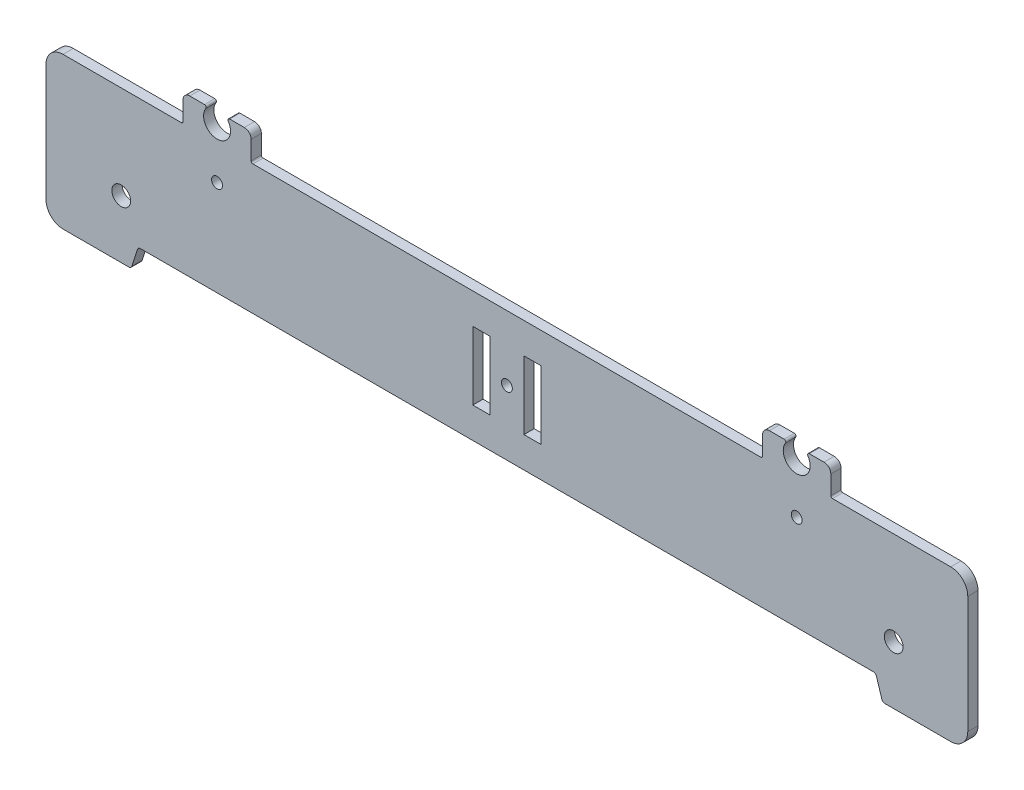
SolidWorks part; units mm, degrees
ref_plane "Alzado" through (0, 0, 0) normal (0, 0, 1) x (1, 0, 0)
ref_plane "Planta" through (0, 0, 0) normal (0, 1, 0) x (1, 0, 0)
ref_plane "Vista lateral" through (0, 0, 0) normal (1, 0, 0) x (0, 0, -1)
sketch "Model" plane through (0, 0, 0) normal (0, 0, 1) x (1, 0, 0)
  line L0 (144.0398, 7.6866) -> (36.5996, 7.689)
  line L1 (35.6453, 6.9878) -> (34.0844, 2.0026)
  line L2 (33.1301, 1.3014) -> (13.8648, 1.3014)
  line L3 (8.8648, 6.3014) -> (8.8648, 40.689)
  line L4 (13.8648, 45.689) -> (18.8648, 45.689)
  line L5 (18.8648, 45.689) -> (48.5373, 45.689)
  line L6 (49.0373, 46.189) -> (49.0373, 51.687)
  line L7 (51.0373, 53.687) -> (55.3535, 53.687)
  line L8 (62.7212, 53.687) -> (67.0373, 53.687)
  line L9 (69.0373, 51.687) -> (69.0373, 46.189)
  line L10 (69.5373, 45.689) -> (144.0398, 45.689)
  line L11 (144.0398, 45.689) -> (218.5423, 45.689)
  line L12 (219.0423, 46.189) -> (219.0423, 51.687)
  line L13 (221.0423, 53.687) -> (225.3585, 53.687)
  line L14 (232.7262, 53.687) -> (237.0423, 53.687)
  line L15 (239.0423, 51.687) -> (239.0423, 46.189)
  line L16 (239.5423, 45.689) -> (269.2148, 45.689)
  line L17 (269.2148, 45.689) -> (274.2148, 45.689)
  line L18 (279.2148, 40.689) -> (279.2148, 6.3014)
  line L19 (274.2148, 1.3014) -> (254.9496, 1.3014)
  line L20 (253.9953, 2.0026) -> (252.4344, 6.9878)
  line L21 (251.4801, 7.689) -> (144.0398, 7.6866)
  line L22 (154.0398, 36.6878) -> (149.0398, 36.6878)
  line L23 (149.0398, 36.6878) -> (149.0398, 16.6878)
  line L24 (149.0398, 16.6878) -> (154.0398, 16.6878)
  line L25 (154.0398, 16.6878) -> (154.0398, 26.6878)
  line L26 (154.0398, 26.6878) -> (154.0398, 36.6878)
  line L27 (134.0398, 36.6878) -> (139.0398, 36.6878)
  line L28 (139.0398, 36.6878) -> (139.0398, 16.6878)
  line L29 (139.0398, 16.6878) -> (134.0398, 16.6878)
  line L30 (134.0398, 16.6878) -> (134.0398, 26.6878)
  line L31 (134.0398, 26.6878) -> (134.0398, 36.6878)
  circle A0 centre (59.0373, 35.6907) radius 1.6
  circle A1 centre (144.0398, 26.6878) radius 1.6
  circle A2 centre (229.0423, 35.6907) radius 1.6
  circle A3 centre (144.0398, 26.6878) radius 1.6
  circle A4 centre (30.9257, 18.3014) radius 2.75
  circle A5 centre (257.4839, 18.3014) radius 2.75
  arc A6 (36.5996, 7.689) -> (35.6453, 6.9878) centre (36.5996, 6.689) ccw
  arc A7 (33.1301, 1.3014) -> (34.0844, 2.0026) centre (33.1301, 2.3014) ccw
  arc A8 (8.8648, 6.3014) -> (13.8648, 1.3014) centre (13.8648, 6.3014) ccw
  arc A9 (13.8648, 45.689) -> (8.8648, 40.689) centre (13.8648, 40.689) ccw
  arc A10 (48.5373, 45.689) -> (49.0373, 46.189) centre (48.5373, 46.189) ccw
  arc A11 (51.0373, 53.687) -> (49.0373, 51.687) centre (51.0373, 51.687) ccw
  arc A12 (55.7674, 52.9065) -> (55.3535, 53.687) centre (55.3535, 53.187) ccw
  arc A13 (55.7674, 52.9065) -> (62.3073, 52.9065) centre (59.0373, 50.6907) ccw
  arc A14 (62.7212, 53.687) -> (62.3073, 52.9065) centre (62.7212, 53.187) ccw
  arc A15 (69.0373, 51.687) -> (67.0373, 53.687) centre (67.0373, 51.687) ccw
  arc A16 (69.0373, 46.189) -> (69.5373, 45.689) centre (69.5373, 46.189) ccw
  arc A17 (218.5423, 45.689) -> (219.0423, 46.189) centre (218.5423, 46.189) ccw
  arc A18 (221.0423, 53.687) -> (219.0423, 51.687) centre (221.0423, 51.687) ccw
  arc A19 (225.7724, 52.9065) -> (225.3585, 53.687) centre (225.3585, 53.187) ccw
  arc A20 (225.7724, 52.9065) -> (232.3123, 52.9065) centre (229.0423, 50.6907) ccw
  arc A21 (232.7262, 53.687) -> (232.3123, 52.9065) centre (232.7262, 53.187) ccw
  arc A22 (239.0423, 51.687) -> (237.0423, 53.687) centre (237.0423, 51.687) ccw
  arc A23 (239.0423, 46.189) -> (239.5423, 45.689) centre (239.5423, 46.189) ccw
  arc A24 (279.2148, 40.689) -> (274.2148, 45.689) centre (274.2148, 40.689) ccw
  arc A25 (274.2148, 1.3014) -> (279.2148, 6.3014) centre (274.2148, 6.3014) ccw
  arc A26 (253.9953, 2.0026) -> (254.9496, 1.3014) centre (254.9496, 2.3014) ccw
  arc A27 (252.4344, 6.9878) -> (251.4801, 7.689) centre (251.4801, 6.689) ccw
extrude "Saliente-Extruir1" add sketch "Model" along normal blind 3 contours A27 L20 A26 L19 A25 L18 A24 L17 L16 A23 L15 A22 L14 A21 A20 A19 L13 A18 L12 A17 L11 L10 A16 L9 A15 L8 A14 A13 A12 L7 A11 L6 A10 L5 L4 A9 L3 A8 L2 A7 L1 A6 L0 L21 A5 A4 A2
